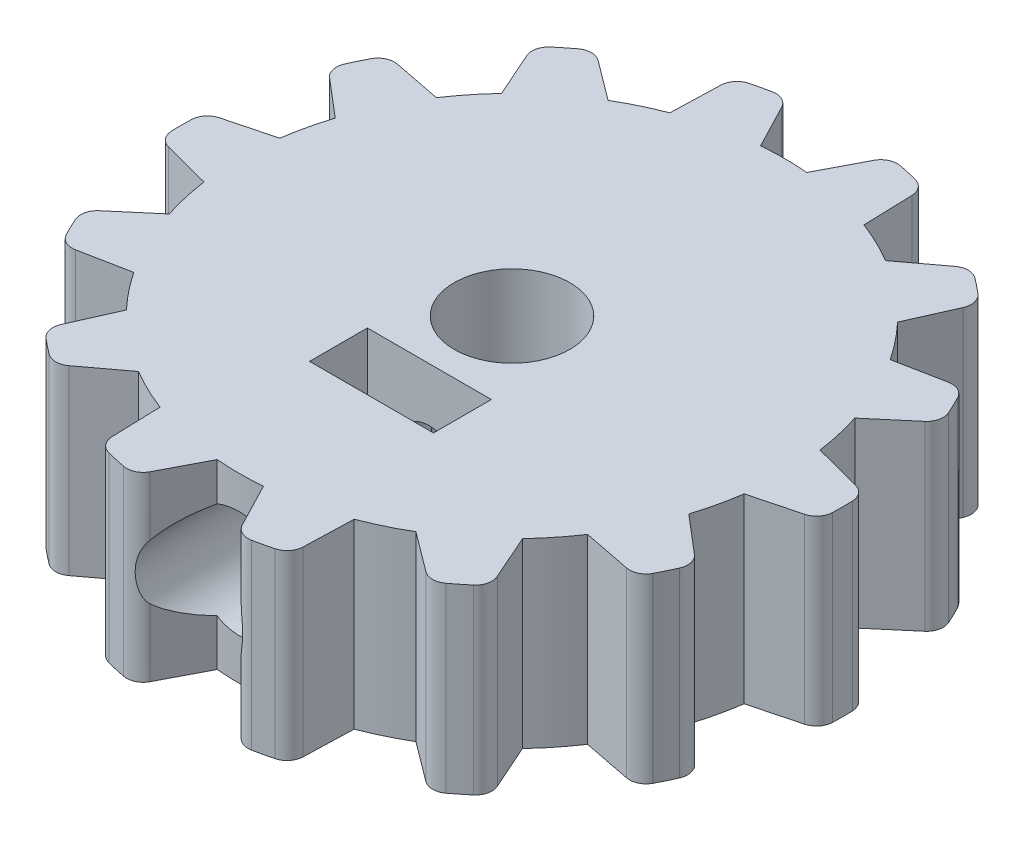
SolidWorks part; units mm, degrees
ref_plane "Front Plane" through (0, 0, 0) normal (0, 0, 1) x (1, 0, 0)
ref_plane "Top Plane" through (0, 0, 0) normal (0, 1, 0) x (1, 0, 0)
ref_plane "Right Plane" through (0, 0, 0) normal (1, 0, 0) x (0, 0, -1)
sketch "Sketch1" plane through (0, 0, 0) normal (0, 1, 0) x (1, 0, 0)
  circle A0 centre (0, 0) radius 20
  dimension "D1" = 40
extrude "Boss-Extrude1" add sketch "Sketch1" along normal blind 11
sketch "Sketch2" plane through (0, 11, 0) normal (0, 1, 0) x (1, 0, 0)
  line L0 (-3.125, 19.7544) -> (-1.3999, 16.4405)
  line L2 (1.3999, 16.4405) -> (3.125, 19.7544)
  circle A0 centre (0, 0) radius 20 construction
  arc A1 (-1.3999, 16.4405) -> (1.3999, 16.4405) centre (0, 0) cw
  arc A2 (3.125, 19.7544) -> (-3.125, 19.7544) centre (0, 0) ccw
  point P6 (0, 16.5)
  dimension "D1" = 16.5
  dimension "D2" = 55
  dimension "D3" = 6.25
extrude "Cut-Extrude1" cut sketch "Sketch2" against normal up to next (11 mm away)
fillet "Fillet1" radius 1 2 edges at (3.125, 5.5, -19.7544) (-3.125, 5.5, -19.7544)
pattern_circular "CirPattern1" count 14 over 360 about axis through (0, 0, 0) along (0, 1, 0) of "Cut-Extrude1", "Fillet1"
sketch "Sketch3" plane through (0, 11, 0) normal (0, 1, 0) x (1, 0, 0)
  circle A0 centre (0, 0) radius 3.5
  dimension "D1" = 3.5
extrude "Cut-Extrude2" cut sketch "Sketch3" against normal up to next
sketch "Sketch4" plane through (0, 11, 0) normal (0, 1, 0) x (1, 0, 0)
  line L1 (-3.75, -5) -> (3.75, -5)
  line L2 (-3.75, -5) -> (-3.75, -8.5)
  line L3 (-3.75, -8.5) -> (3.75, -8.5)
  line L4 (3.75, -5) -> (3.75, -8.5)
  point P4 (0, -5)
  dimension "D1" = 5
  dimension "D2" = 3.5
  dimension "D3" = 7.5
extrude "Cut-Extrude3" cut sketch "Sketch4" against normal blind 9
sketch "Sketch6" plane through (0, 0, 0) normal (1, 0, 0) x (0, 0, -1)
  line L0 (0, 5.75) -> (-29.7973, 5.75) construction
  line L1 (-8.5, 2) -> (-5, 2) construction
  line L2 (0, 5.75) -> (0, 7.75)
  line L3 (0, 7.75) -> (-10, 7.75)
  line L4 (-10, 7.75) -> (-10, 9)
  line L5 (-10, 9) -> (-25, 9)
  line L6 (-25, 9) -> (-25, 5.75)
  line L7 (-25, 5.75) -> (0, 5.75)
  dimension "D1" = 3.75
  dimension "D2" = 4
  dimension "D3" = 6.5
  dimension "D4" = 10
  dimension "D5" = 25
revolve "Cut-Revolve1" cut sketch "Sketch6" angle 360 about L0
